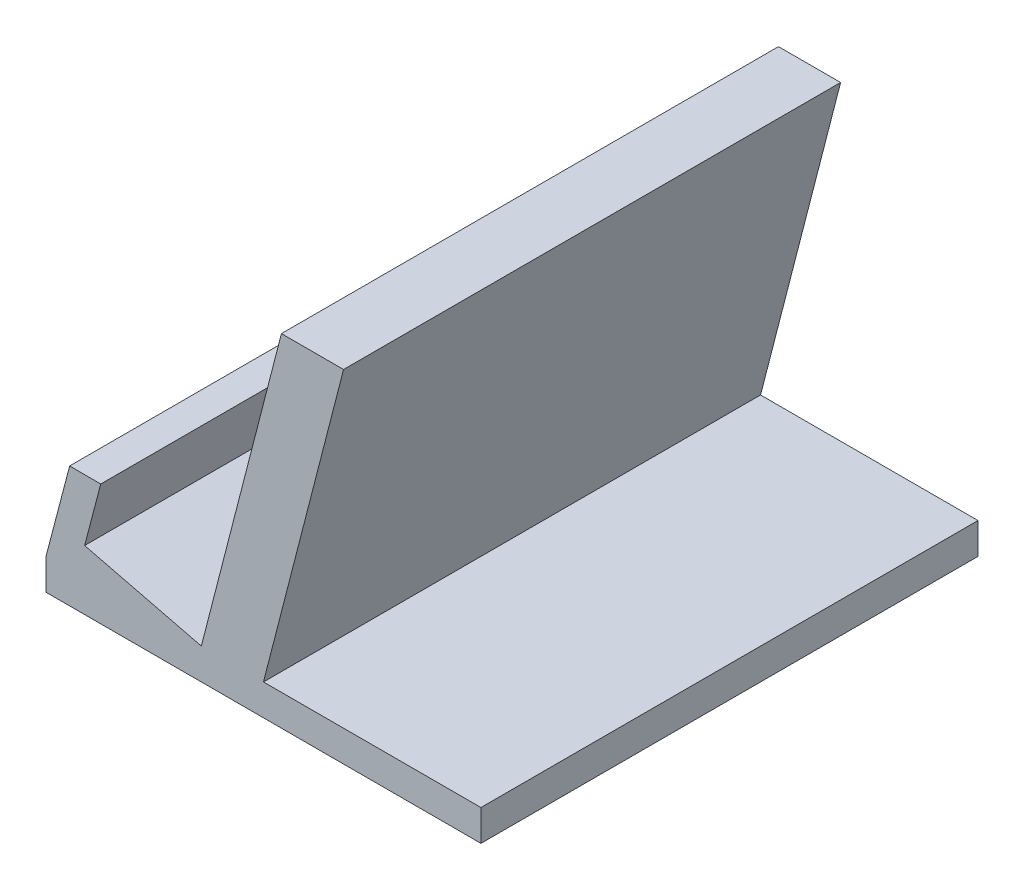
SolidWorks part; units mm, degrees
ref_plane "前基準面" through (0, 0, 0) normal (0, 0, 1) x (1, 0, 0)
ref_plane "上基準面" through (0, 0, 0) normal (0, 1, 0) x (1, 0, 0)
ref_plane "右基準面" through (0, 0, 0) normal (1, 0, 0) x (0, 0, -1)
sketch "草圖1" plane through (0, 0, 0) normal (0, 0, 1) x (1, 0, 0)
  line L0 (-10.0454, -0.2709) -> (2.8438, 49.7291)
  line L1 (-35.0454, -5.2709) -> (34.9546, -5.2709)
  line L2 (-35.0454, -5.2709) -> (-35.0454, -0.2709)
  line L3 (-35.0454, -0.2709) -> (34.9546, -0.2709)
  line L4 (34.9546, -5.2709) -> (34.9546, -0.2709)
  line L13 (-10.0454, -0.2709) -> (-0.0454, -0.2709)
  line L14 (2.8438, 49.7291) -> (12.8438, 49.7291)
  line L15 (-0.0454, -0.2709) -> (12.8438, 49.7291)
  line L16 (-35.0454, -0.2709) -> (-31.2397, 14.2413)
  line L17 (-35.0454, -0.2709) -> (-30.0455, -0.2894)
  line L18 (-31.2397, 14.2413) -> (-26.2397, 14.2229)
  line L20 (-10.0454, -0.2709) -> (-28.8274, 4.3554)
  line L21 (-26.2397, 14.2229) -> (-28.8274, 4.3554)
  dimension "D1" = 70
  dimension "D2" = 5
  dimension "D3" = 25
  dimension "D4" = 10
  dimension "D5" = 5
  dimension "D6" = 50
extrude "填料-伸長4" add sketch "草圖1" along normal blind 80
